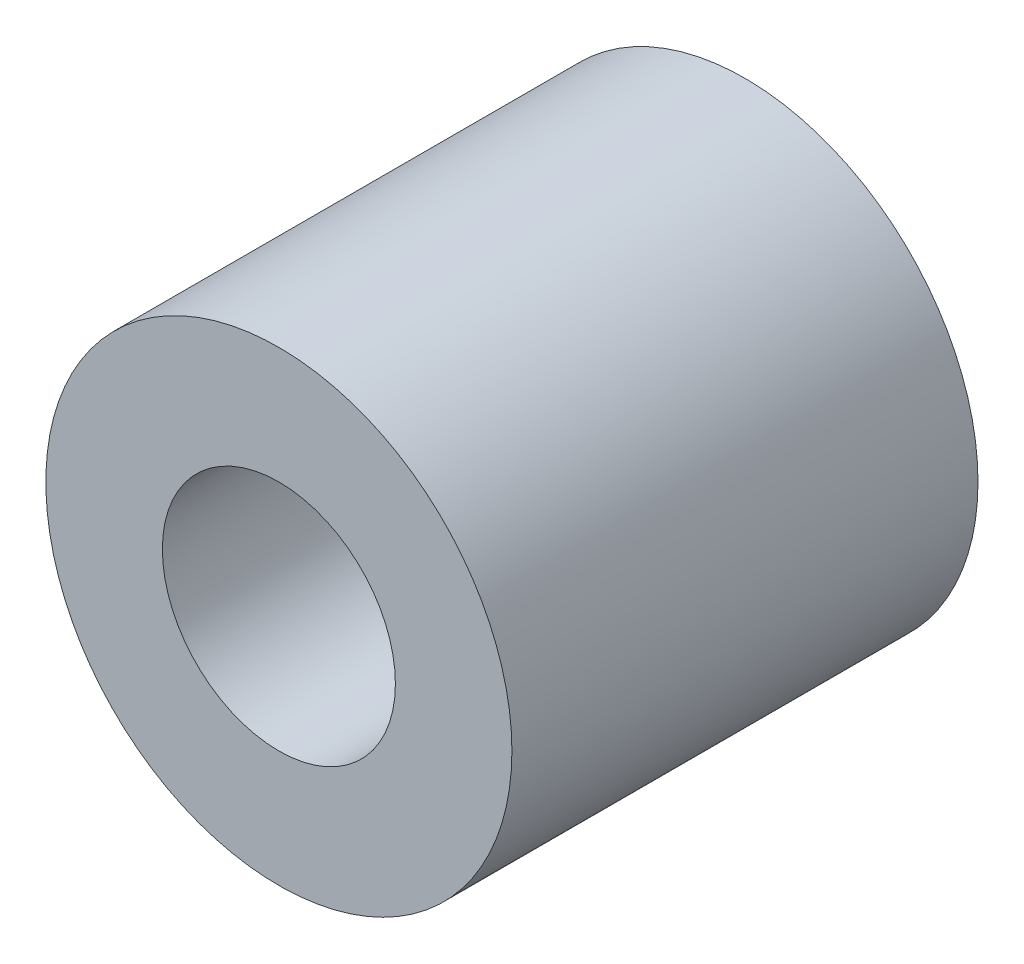
SolidWorks part; units mm, degrees
ref_plane "前视基准面" through (0, 0, 0) normal (0, 0, 1) x (1, 0, 0)
ref_plane "上视基准面" through (0, 0, 0) normal (0, 1, 0) x (1, 0, 0)
ref_plane "右视基准面" through (0, 0, 0) normal (1, 0, 0) x (0, 0, -1)
sketch "草图1" plane through (0, 0, 0) normal (0, 0, 1) x (1, 0, 0)
  circle A0 centre (0, 0) radius 6
  circle A1 centre (0, 0) radius 3
  dimension "D1" = 6
  dimension "D2" = 12
extrude "凸台-拉伸1" add sketch "草图1" along normal blind 12
